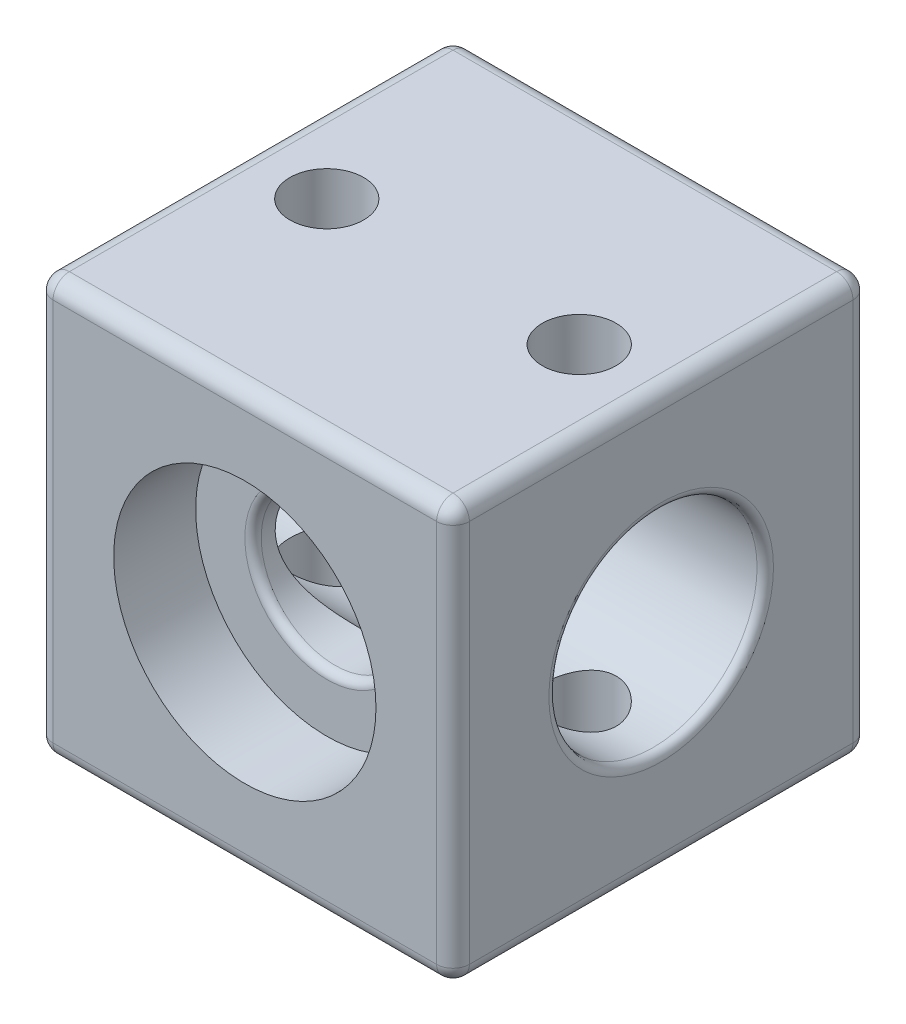
SolidWorks part; units mm, degrees
ref_plane "Front Plane" through (0, 0, 0) normal (0, 0, 1) x (1, 0, 0)
ref_plane "Top Plane" through (0, 0, 0) normal (0, 1, 0) x (1, 0, 0)
ref_plane "Right Plane" through (0, 0, 0) normal (1, 0, 0) x (0, 0, -1)
sketch "Sketch1" plane through (0, 0, 0) normal (1, 0, 0) x (0, 0, -1)
  line L1 (12.7, -12.7) -> (-12.7, -12.7)
  line L2 (12.7, -12.7) -> (12.7, 12.7)
  line L3 (12.7, 12.7) -> (-12.7, 12.7)
  line L4 (-12.7, -12.7) -> (-12.7, 12.7)
  line L5 (12.7, -12.7) -> (-12.7, 12.7) construction
  line L6 (12.7, 12.7) -> (-12.7, -12.7) construction
  circle A0 centre (0, 0) radius 6.35
  dimension "D1" = 12.7
  dimension "D2" = 25.4
extrude "Boss-Extrude1" add sketch "Sketch1" along normal blind 25.4
sketch "Sketch2" plane through (0, 0, 12.7) normal (0, 0, 1) x (1, 0, 0)
  line L0 (0, 12.7) -> (25.4, -12.7) construction
  circle A0 centre (12.7, 0) radius 8
  point P6 (0, 0)
  dimension "D1" = 16
extrude "Cut-Extrude2" cut sketch "Sketch2" against normal blind 5
mirror "Mirror1" about plane through (0, 0, 0) normal (0, 0, 1) of "Cut-Extrude2"
sketch "Sketch3" plane through (0, 0, 7.7) normal (0, 0, 1) x (1, 0, 0)
  circle A0 centre (12.7, 0) radius 4.5
  circle A1 centre (12.7, 0) radius 8 construction
  circle A2 centre (12.7, 0) radius 8 construction
  point P5 (0, 0)
  point P6 (0, 0)
  dimension "D1" = 9
extrude "Cut-Extrude3" cut sketch "Sketch3" against normal blind 44
fillet "Fillet1" radius 1 12 edges at (12.7, -12.7, 12.7) (25.4, -12.7, 0) (12.7, -12.7, -12.7) (0, -12.7, 0) (12.7, 12.7, -12.7) (25.4, 12.7, 0) (12.7, 12.7, 12.7) (0, 12.7, 0) (0, 0, -12.7) (0, 0, 12.7) (25.4, 0, -12.7) (25.4, 0, 12.7)
fillet "Fillet2" radius 0.5 4 edges at (8.2, 0, -7.7) (17.2, 0, 7.7) (25.4, 0, -6.35) (0, 0, -6.35)
sketch "Sketch4" plane through (0, 12.7, 0) normal (0, 1, 0) x (1, 0, 0)
  line L0 (12.7, 11.7) -> (12.7, -11.7) construction
  line L1 (24.4, 11.7) -> (1, 11.7) construction
  line L2 (1, -11.7) -> (24.4, -11.7) construction
  circle A0 centre (5, 0) radius 2.25
  circle A1 centre (20.4, 0) radius 2.25
  point P8 (0, 0)
  dimension "D2" = 4.5
  dimension "D1" = 5
extrude "Cut-Extrude4" cut sketch "Sketch4" against normal blind 44
sketch "Sketch5" plane through (0, -12.7, 0) normal (0, -1, 0) x (1, 0, 0)
  line L1 (9, 2.3094) -> (5, 4.6188)
  line L2 (5, 4.6188) -> (1, 2.3094)
  line L3 (1, 2.3094) -> (1, -2.3094)
  line L4 (1, -2.3094) -> (5, -4.6188)
  line L5 (5, -4.6188) -> (9, -2.3094)
  line L6 (9, -2.3094) -> (9, 2.3094)
  line L7 (20.4, 4.6188) -> (16.4, 2.3094)
  line L8 (16.4, 2.3094) -> (16.4, -2.3094)
  line L9 (16.4, -2.3094) -> (20.4, -4.6188)
  line L10 (20.4, -4.6188) -> (24.4, -2.3094)
  line L11 (24.4, -2.3094) -> (24.4, 2.3094)
  line L12 (24.4, 2.3094) -> (20.4, 4.6188)
  circle A0 centre (5, 0) radius 4 construction
  circle A1 centre (20.4, 0) radius 2.25 construction
  circle A2 centre (20.4, 0) radius 2.25 construction
  circle A3 centre (20.4, 0) radius 4 construction
  dimension "D1" = 8
extrude "Cut-Extrude5" cut sketch "Sketch5" against normal blind 1
